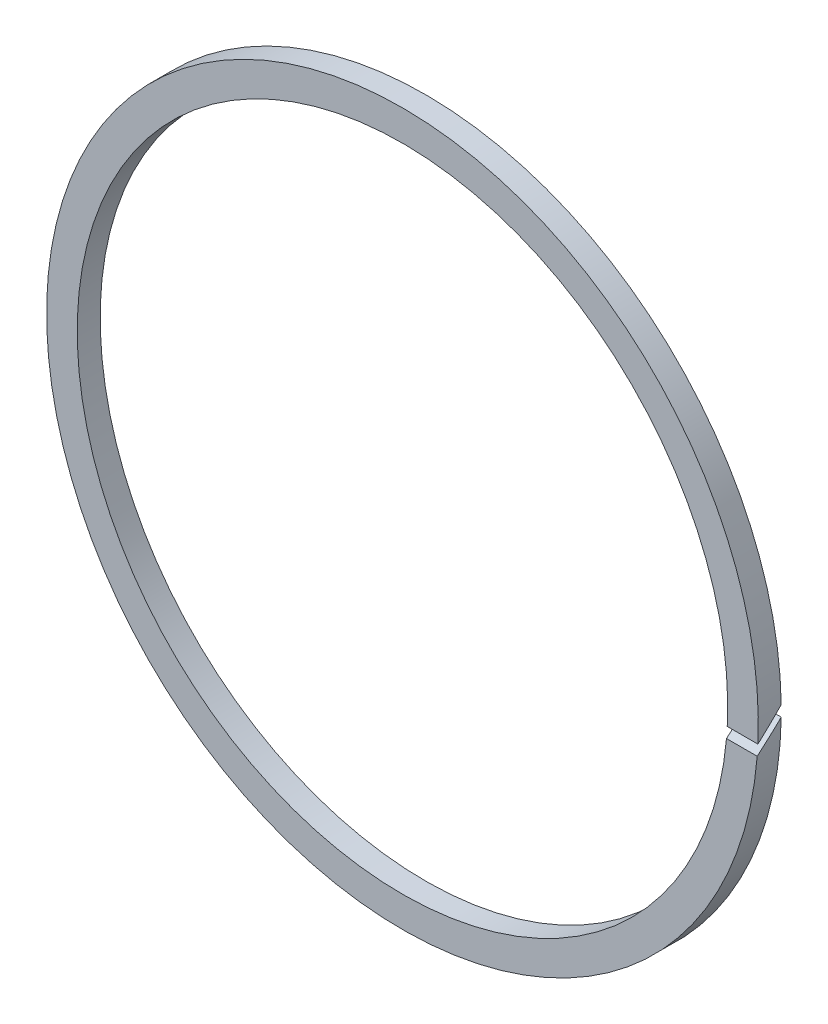
SolidWorks part; units mm, degrees
ref_plane "Front Plane" through (0, 0, 0) normal (0, 0, 1) x (1, 0, 0)
ref_plane "Top Plane" through (0, 0, 0) normal (0, 1, 0) x (1, 0, 0)
ref_plane "Right Plane" through (0, 0, 0) normal (1, 0, 0) x (0, 0, -1)
sketch "Sketch1" plane through (0, 0, 0) normal (0, 0, 1) x (1, 0, 0)
  circle A0 centre (0, 0) radius 42.5
  circle A1 centre (0, 0) radius 46.5
  dimension "D1" = 85
  dimension "D2" = 93
extrude "Boss-Extrude1" add sketch "Sketch1" along normal blind 3
sketch "Sketch2" plane through (0, 0, 0) normal (1, 0, 0) x (0, 0, -1)
  line L0 (-17.2013, -17.2013) -> (17.2013, 17.2013) construction
  line L1 (-1.5, 49.8163) -> (-1.5, -50.099) construction
  line L2 (-3, 46.5) -> (-3, -46.5) construction
  line L3 (0, -46.5) -> (0, 46.5) construction
  line L4 (-14.6089, -13.9018) -> (14.3772, 15.0843)
  line L5 (-13.9018, -14.6089) -> (15.0843, 14.3772)
  line L6 (-14.6089, -13.9018) -> (-13.9018, -14.6089)
  line L7 (14.3772, 15.0843) -> (15.0843, 14.3772)
  point P2 (0, 0)
  dimension "D1" = 135
  dimension "D2" = 0.5
extrude "Cut-Extrude2" cut sketch "Sketch2" along normal up to surface (43.9854 mm away)
